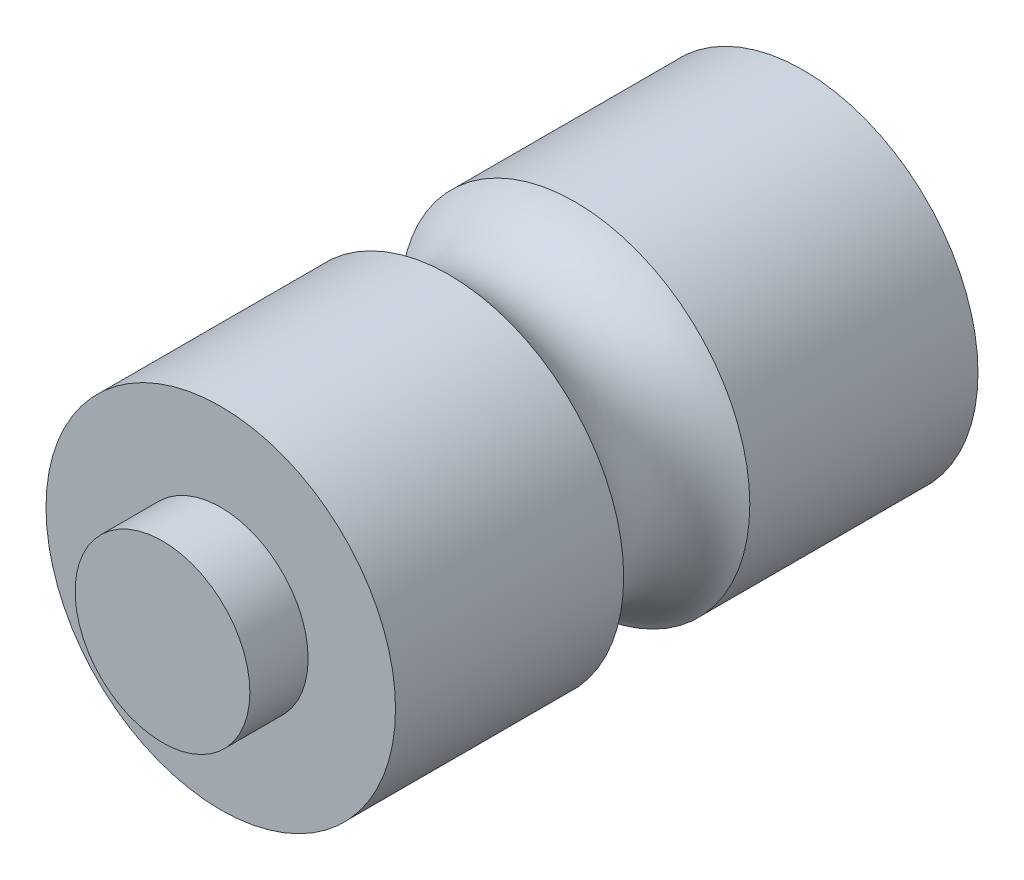
SolidWorks part; units mm, degrees
ref_plane "Front Plane" through (0, 0, 0) normal (0, 0, 1) x (1, 0, 0)
ref_plane "Top Plane" through (0, 0, 0) normal (0, 1, 0) x (1, 0, 0)
ref_plane "Right Plane" through (0, 0, 0) normal (1, 0, 0) x (0, 0, -1)
sketch "Sketch1" plane through (0, 0, 0) normal (0, 0, 1) x (1, 0, 0)
  circle A0 centre (0, 0) radius 7.62
extrude "Boss-Extrude1" add sketch "Sketch1" along normal blind 25.4
sketch "Sketch2" plane through (0, 0, 0) normal (0, 1, 0) x (1, 0, 0)
  line L5 (7.62, -9.9504) -> (7.62, -15.4496)
  arc A0 (7.62, -9.9504) -> (7.62, -15.4496) centre (9.2075, -12.7) ccw
sweep "Cut-Sweep1" cut profiles "Sketch2" path edge at (7.62, 0, 0)
sketch "Sketch3" plane through (0, 0, 25.4) normal (0, 0, 1) x (1, 0, 0)
  circle A0 centre (0, 0) radius 3.81
extrude "Boss-Extrude2" add sketch "Sketch3" along normal blind 2.54
sketch "Sketch4" plane through (0, 0, 0) normal (0, 0, -1) x (-1, 0, 0)
  circle A0 centre (0, 0) radius 3.81
extrude "Boss-Extrude3" add sketch "Sketch4" along normal blind 2.54
